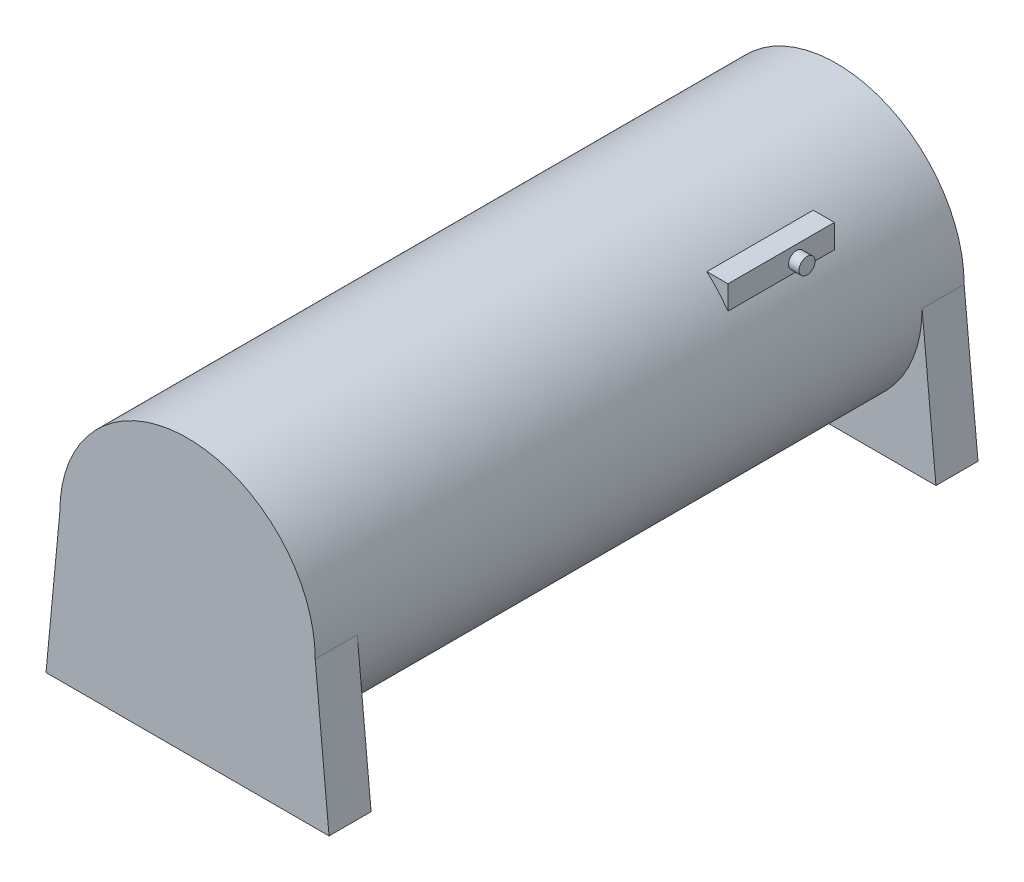
SolidWorks part; units mm, degrees
ref_plane "Front Plane" through (0, 0, 0) normal (0, 0, 1) x (1, 0, 0)
ref_plane "Top Plane" through (0, 0, 0) normal (0, 1, 0) x (1, 0, 0)
ref_plane "Right Plane" through (0, 0, 0) normal (1, 0, 0) x (0, 0, -1)
sketch "Sketch1" plane through (0, 0, 0) normal (0, 0, 1) x (1, 0, 0)
  circle A0 centre (0, 0) radius 60.72
  dimension "D1" = 121.44
extrude "Boss-Extrude1" add sketch "Sketch1" along normal blind 308.6
sketch "Sketch2" plane through (0, 0, 308.6) normal (0, 0, 1) x (1, 0, 0)
  line L1 (67.3, -69.5124) -> (-67.3, -69.5124)
  line L2 (-67.3, -69.5124) -> (-60.72, 0)
  line L3 (-60.72, 0) -> (60.72, 0)
  line L4 (67.3, -69.5124) -> (60.72, 0)
  circle A0 centre (0, 0) radius 60.72 construction
extrude "Boss-Extrude2" add sketch "Sketch2" against normal blind 20
sketch "Sketch3" plane through (0, 0, 0) normal (0, 0, -1) x (-1, 0, 0)
  line L1 (67.3, -69.5124) -> (-67.3, -69.5124) construction
  line L2 (2.237, -69.5124) -> (-67.3, -69.5124)
  line L3 (-67.3, -69.5124) -> (-60.72, 0)
  line L4 (-60.72, 0) -> (60.72, 0)
  line L5 (60.72, 0) -> (67.3, -69.5124)
  line L6 (67.3, -69.5124) -> (2.237, -69.5124)
extrude "Boss-Extrude3" add sketch "Sketch3" against normal blind 20
ref_plane "Plane1" through (50, 0, 0) normal (1, 0, 0) x (0, 0, -1)
sketch "Sketch4" plane through (50, 0, 0) normal (1, 0, 0) x (0, 0, -1)
  line L0 (0, 0) -> (0, 60.72) construction
  line L1 (-101.6, 45.72) -> (-51, 45.72)
  line L2 (-101.6, 45.72) -> (-101.6, 33.02)
  line L3 (-101.6, 33.02) -> (-51, 33.02)
  line L4 (-51, 45.72) -> (-51, 33.02)
  line L5 (0, 60.72) -> (-308.6, 60.72) construction
  dimension "D1" = 50.6
  dimension "D2" = 12.7
  dimension "D3" = 101.6
  dimension "D4" = 15
extrude "Boss-Extrude4" add sketch "Sketch4" against normal blind 20
sketch "Sketch5" plane through (50, 0, 0) normal (1, 0, 0) x (0, 0, -1)
  line L0 (-51, 34.4517) -> (-51, 45.72) construction
  line L1 (-51, 45.72) -> (-101.6, 45.72) construction
  circle A0 centre (-69, 39.37) radius 3.8
  dimension "D1" = 7.6
  dimension "D2" = 18
  dimension "D3" = 6.35
extrude "Boss-Extrude5" add sketch "Sketch5" along normal blind 5
